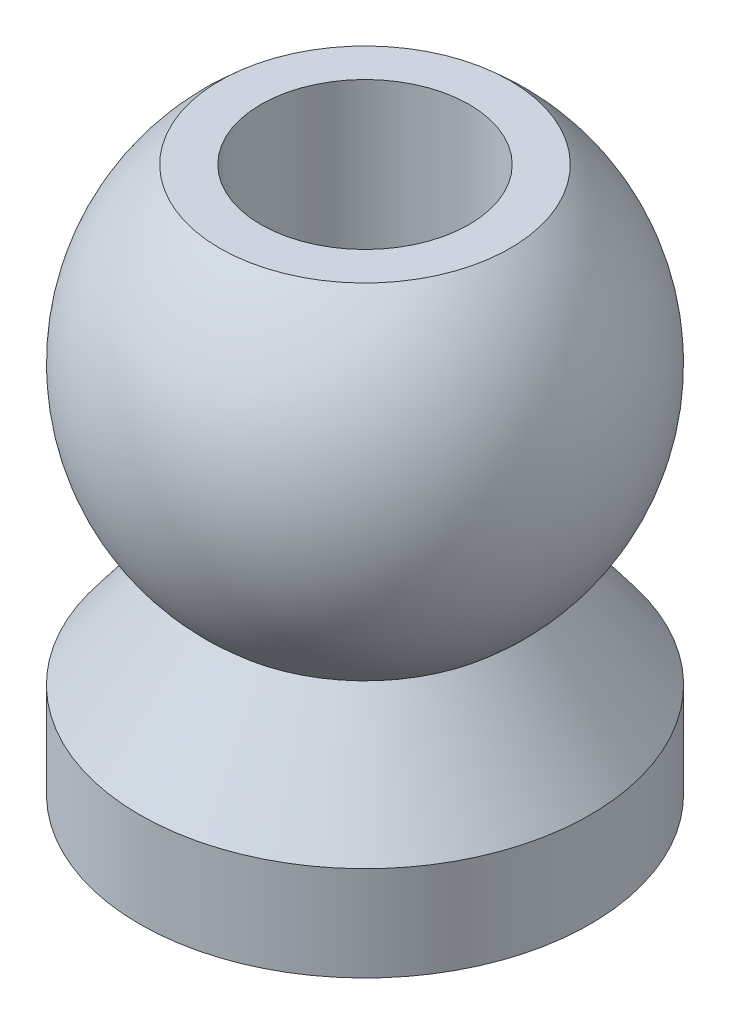
SolidWorks part; units mm, degrees
material "Brass"
ref_plane "Front Plane" through (0, 0, 0) normal (0, 0, 1) x (1, 0, 0)
ref_plane "Top Plane" through (0, 0, 0) normal (0, 1, 0) x (1, 0, 0)
ref_plane "Right Plane" through (0, 0, 0) normal (1, 0, 0) x (0, 0, -1)
sketch "Sketch2" plane through (0, 0, 0) normal (0, 0, 1) x (1, 0, 0)
  line L0 (0, 4.3805) -> (0, -5.41) construction
  line L1 (-1.1, -3.94) -> (-2.38, -3.94)
  line L2 (-2.38, -3.94) -> (-2.38, -2.94)
  line L3 (-2.38, -2.94) -> (-1.5336, -1.82)
  line L5 (-1.5336, -1.82) -> (0, -1.82) construction
  line L6 (-1.1, 1.82) -> (-1.5336, 1.82)
  line L8 (-1.1, 1.82) -> (-1.1, -3.94)
  circle A0 centre (0, 0) radius 2.38 construction
  arc A1 (-1.5336, 1.82) -> (-1.5336, -1.82) centre (0, 0) ccw
  dimension "D1" = 4.76
  dimension "D2" = 3.64
  dimension "D3" = 2.12
  dimension "D4" = 2.38
  dimension "D5" = 1.1
  dimension "D6" = 1
revolve "Revolve2" add sketch "Sketch2" angle 360 about L0
